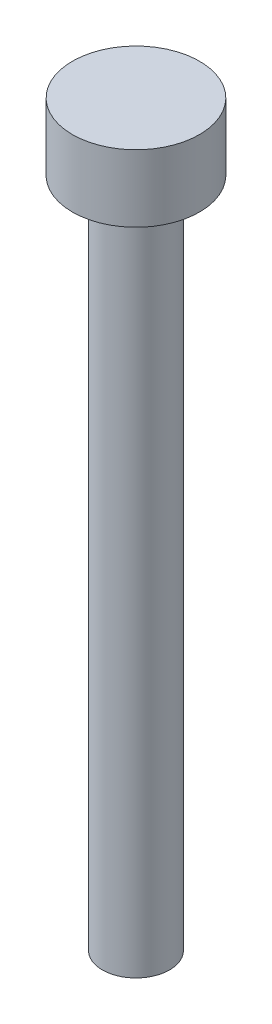
SolidWorks part; units mm, degrees
ref_plane "Alzado" through (0, 0, 0) normal (0, 0, 1) x (1, 0, 0)
ref_plane "Planta" through (0, 0, 0) normal (0, 1, 0) x (1, 0, 0)
ref_plane "Vista lateral" through (0, 0, 0) normal (1, 0, 0) x (0, 0, -1)
sketch "Croquis1" plane through (0, 0, 0) normal (0, 1, 0) x (1, 0, 0)
  circle A0 centre (0, 0) radius 1.5
  dimension "D1" = 3
extrude "Saliente-Extruir1" add sketch "Croquis1" along normal blind 30
sketch "Croquis2" plane through (0, 30, 0) normal (0, 1, 0) x (1, 0, 0)
  circle A0 centre (0, 0) radius 2.84
  dimension "D1" = 5.68
extrude "Saliente-Extruir2" add sketch "Croquis2" along normal blind 3
